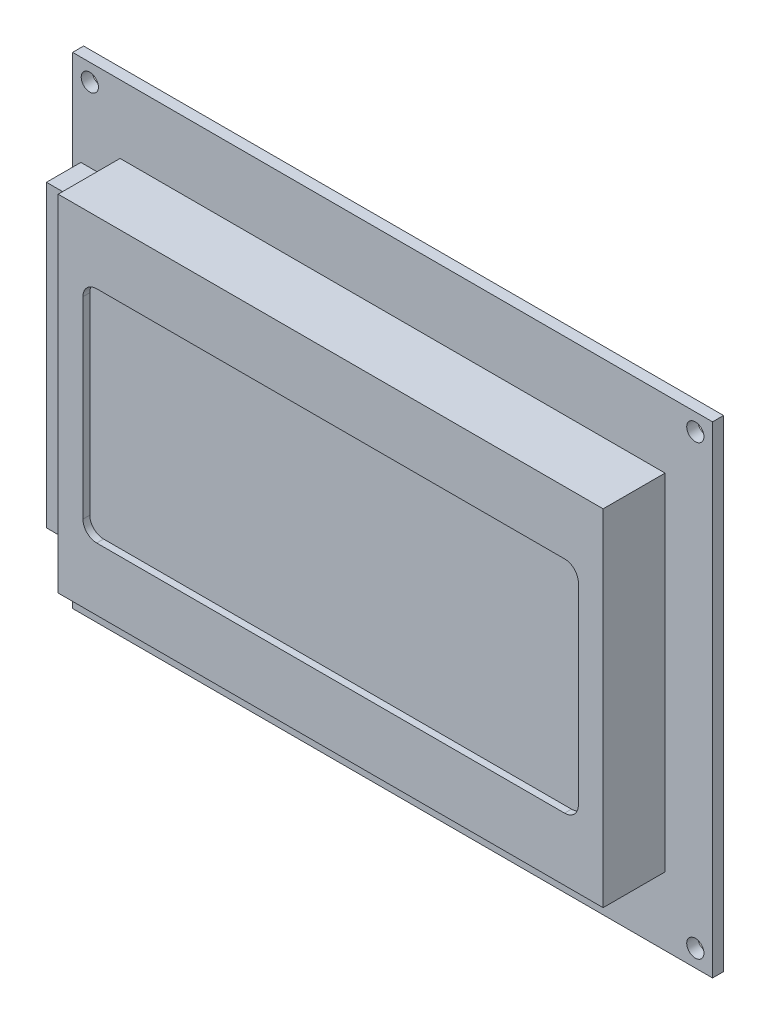
SolidWorks part; units mm, degrees
ref_plane "Plano frontal" through (0, 0, 0) normal (0, 0, 1) x (1, 0, 0)
ref_plane "Plano superior" through (0, 0, 0) normal (0, 1, 0) x (1, 0, 0)
ref_plane "Plano direito" through (0, 0, 0) normal (1, 0, 0) x (0, 0, -1)
sketch "Esboço1" plane through (0, 0, 0) normal (0, 0, 1) x (1, 0, 0)
  line L0 (-35, -33) -> (13.26, -33) construction
  line L1 (-46.5, -35) -> (46.5, -35)
  line L2 (-46.5, -35) -> (-46.5, 35)
  line L3 (-46.5, 35) -> (46.5, 35)
  line L4 (46.5, -35) -> (46.5, 35)
  line L5 (-46.5, -35) -> (46.5, 35) construction
  line L6 (-46.5, 35) -> (46.5, -35) construction
  line L7 (-44, -32.5) -> (44, -32.5) construction
  line L8 (-44, -32.5) -> (-44, 32.5) construction
  line L9 (-44, 32.5) -> (44, 32.5) construction
  line L10 (44, -32.5) -> (44, 32.5) construction
  line L11 (-44, -32.5) -> (44, 32.5) construction
  line L12 (-44, 32.5) -> (44, -32.5) construction
  line L13 (-39.6, -25.1) -> (39.6, -25.1)
  line L14 (-39.6, -25.1) -> (-39.6, 25.1)
  line L15 (-39.6, 25.1) -> (39.6, 25.1)
  line L16 (39.6, -25.1) -> (39.6, 25.1)
  line L17 (-39.6, -25.1) -> (39.6, 25.1) construction
  line L18 (-39.6, 25.1) -> (39.6, -25.1) construction
  line L19 (-34, -16) -> (34, -16)
  line L20 (-36, -14) -> (-36, 14)
  line L21 (-34, 16) -> (34, 16)
  line L22 (36, -14) -> (36, 14)
  line L23 (-36, -16) -> (36, 16) construction
  line L24 (-36, 16) -> (36, -16) construction
  line L26 (-45.3, -21.75) -> (-39.6, -21.75)
  line L27 (-45.3, -21.75) -> (-45.3, 21.75)
  line L28 (-45.3, 21.75) -> (-39.6, 21.75)
  line L29 (-39.6, -21.75) -> (-39.6, 21.75)
  line L30 (-45.3, -21.75) -> (-39.6, 21.75) construction
  line L31 (-45.3, 21.75) -> (-39.6, -21.75) construction
  circle A0 centre (-44, 32.5) radius 1.25
  circle A1 centre (44, 32.5) radius 1.25
  circle A2 centre (44, -32.5) radius 1.25
  circle A3 centre (-44, -32.5) radius 1.25
  arc A4 (-34, 16) -> (-36, 14) centre (-34, 14) ccw
  arc A5 (36, 14) -> (34, 16) centre (34, 14) ccw
  arc A6 (36, -14) -> (34, -16) centre (34, -14) cw
  arc A7 (-34, -16) -> (-36, -14) centre (-34, -14) cw
  circle A8 centre (-35, -33) radius 0.5
  circle A9 centre (13.26, -33) radius 0.5
  circle A10 centre (-32.46, -33) radius 0.5
  circle A11 centre (-29.92, -33) radius 0.5
  circle A12 centre (-27.38, -33) radius 0.5
  circle A13 centre (-24.84, -33) radius 0.5
  circle A14 centre (-22.3, -33) radius 0.5
  circle A15 centre (-19.76, -33) radius 0.5
  circle A16 centre (-17.22, -33) radius 0.5
  circle A17 centre (-14.68, -33) radius 0.5
  circle A18 centre (-12.14, -33) radius 0.5
  circle A19 centre (-9.6, -33) radius 0.5
  circle A20 centre (-7.06, -33) radius 0.5
  circle A21 centre (-4.52, -33) radius 0.5
  circle A22 centre (-1.98, -33) radius 0.5
  circle A23 centre (0.56, -33) radius 0.5
  circle A24 centre (3.1, -33) radius 0.5
  circle A25 centre (5.64, -33) radius 0.5
  circle A26 centre (8.18, -33) radius 0.5
  circle A27 centre (10.72, -33) radius 0.5
  point P0 (0, 0)
  point P7 (0, 0)
  point P8 (0, 0)
  point P16 (0, 0)
  point P21 (0, 0)
  point P78 (-42.45, 0)
  dimension "D5" = 2.5
  dimension "D6" = 2.5
  dimension "D7" = 2.5
  dimension "D8" = 2.5
  dimension "D13" = 2
  dimension "D14" = 2
  dimension "D15" = 2
  dimension "D16" = 2
  dimension "D17" = 11.5
  dimension "D18" = 2
  dimension "D19" = 1
  dimension "D21" = 1
  dimension "D22" = 2.54
  dimension "D23" = 2.54
  dimension "D24" = 2.54
  dimension "D25" = 2.54
  dimension "D26" = 2.54
  dimension "D27" = 1
  dimension "D28" = 1
  dimension "D29" = 1
  dimension "D30" = 1
  dimension "D31" = 1
  dimension "D32" = 2.54
  dimension "D33" = 2.54
  dimension "D34" = 2.54
  dimension "D45" = 1
  dimension "D46" = 1
  dimension "D47" = 1
  dimension "D48" = 1
  dimension "D49" = 1
  dimension "D50" = 1
  dimension "D51" = 1
  dimension "D52" = 1
  dimension "D53" = 1
  dimension "D54" = 1
  dimension "D55" = 1
  dimension "D56" = 1
  dimension "D57" = 1
  dimension "D1" = 70
  dimension "D2" = 93
  dimension "D3" = 88
  dimension "D4" = 65
  dimension "D9" = 79.2
  dimension "D10" = 50.2
  dimension "D11" = 72
  dimension "D12" = 32
  dimension "D20" = 48.26
  dimension "D35" = 2.54
  dimension "D36" = 2.54
  dimension "D37" = 2.54
  dimension "D38" = 2.54
  dimension "D39" = 2.54
  dimension "D40" = 2.54
  dimension "D41" = 2.54
  dimension "D42" = 2.54
  dimension "D43" = 2.54
  dimension "D44" = 2.54
  dimension "D58" = 5.7
  dimension "D59" = 43.5
extrude "Boss-Extrude1" add sketch "Esboço1" along normal blind 8 contours A7 L19 A6 L22 A5 L21 A4 L20
sketch "Sketch1" plane through (0, 0, 0) normal (0, 0, 1) x (1, 0, 0)
  line L0 (-35, -33) -> (13.26, -33) construction
  line L1 (-46.5, -35) -> (46.5, -35)
  line L2 (-46.5, -35) -> (-46.5, 35)
  line L3 (-46.5, 35) -> (46.5, 35)
  line L4 (46.5, -35) -> (46.5, 35)
  line L5 (-46.5, -35) -> (46.5, 35) construction
  line L6 (-46.5, 35) -> (46.5, -35) construction
  line L7 (-44, -32.5) -> (44, -32.5) construction
  line L8 (-44, -32.5) -> (-44, 32.5) construction
  line L9 (-44, 32.5) -> (44, 32.5) construction
  line L10 (44, -32.5) -> (44, 32.5) construction
  line L11 (-44, -32.5) -> (44, 32.5) construction
  line L12 (-44, 32.5) -> (44, -32.5) construction
  line L13 (-39.6, -25.1) -> (39.6, -25.1)
  line L14 (-39.6, -25.1) -> (-39.6, 25.1)
  line L15 (-39.6, 25.1) -> (39.6, 25.1)
  line L16 (39.6, -25.1) -> (39.6, 25.1)
  line L17 (-39.6, -25.1) -> (39.6, 25.1) construction
  line L18 (-39.6, 25.1) -> (39.6, -25.1) construction
  line L19 (-34, -16) -> (34, -16)
  line L20 (-36, -14) -> (-36, 14)
  line L21 (-34, 16) -> (34, 16)
  line L22 (36, -14) -> (36, 14)
  line L23 (-36, -16) -> (36, 16) construction
  line L24 (-36, 16) -> (36, -16) construction
  line L25 (-45.3, -21.75) -> (-39.6, -21.75)
  line L26 (-45.3, -21.75) -> (-45.3, 21.75)
  line L27 (-45.3, 21.75) -> (-39.6, 21.75)
  line L28 (-39.6, -21.75) -> (-39.6, 21.75)
  line L29 (-45.3, -21.75) -> (-39.6, 21.75) construction
  line L30 (-45.3, 21.75) -> (-39.6, -21.75) construction
  circle A0 centre (-44, 32.5) radius 1.25
  circle A1 centre (44, 32.5) radius 1.25
  circle A2 centre (44, -32.5) radius 1.25
  circle A3 centre (-44, -32.5) radius 1.25
  arc A4 (-34, 16) -> (-36, 14) centre (-34, 14) ccw
  arc A5 (36, 14) -> (34, 16) centre (34, 14) ccw
  arc A6 (36, -14) -> (34, -16) centre (34, -14) cw
  arc A7 (-34, -16) -> (-36, -14) centre (-34, -14) cw
  circle A8 centre (-35, -33) radius 0.5
  circle A9 centre (13.26, -33) radius 0.5
  circle A10 centre (-32.46, -33) radius 0.5
  circle A11 centre (-29.92, -33) radius 0.5
  circle A12 centre (-27.38, -33) radius 0.5
  circle A13 centre (-24.84, -33) radius 0.5
  circle A14 centre (-22.3, -33) radius 0.5
  circle A15 centre (-19.76, -33) radius 0.5
  circle A16 centre (-17.22, -33) radius 0.5
  circle A17 centre (-14.68, -33) radius 0.5
  circle A18 centre (-12.14, -33) radius 0.5
  circle A19 centre (-9.6, -33) radius 0.5
  circle A20 centre (-7.06, -33) radius 0.5
  circle A21 centre (-4.52, -33) radius 0.5
  circle A22 centre (-1.98, -33) radius 0.5
  circle A23 centre (0.56, -33) radius 0.5
  circle A24 centre (3.1, -33) radius 0.5
  circle A25 centre (5.64, -33) radius 0.5
  circle A26 centre (8.18, -33) radius 0.5
  circle A27 centre (10.72, -33) radius 0.5
  point P0 (0, 0)
  point P6 (0, 0)
  point P7 (0, 0)
  point P15 (0, 0)
  point P20 (0, 0)
  point P77 (-42.45, 0)
  dimension "D5" = 2.5
  dimension "D6" = 2.5
  dimension "D7" = 2.5
  dimension "D8" = 2.5
  dimension "D13" = 2
  dimension "D14" = 2
  dimension "D15" = 2
  dimension "D16" = 2
  dimension "D19" = 1
  dimension "D21" = 1
  dimension "D27" = 1
  dimension "D28" = 1
  dimension "D29" = 1
  dimension "D30" = 1
  dimension "D31" = 1
  dimension "D45" = 1
  dimension "D46" = 1
  dimension "D47" = 1
  dimension "D48" = 1
  dimension "D49" = 1
  dimension "D50" = 1
  dimension "D51" = 1
  dimension "D52" = 1
  dimension "D53" = 1
  dimension "D54" = 1
  dimension "D55" = 1
  dimension "D56" = 1
  dimension "D57" = 1
  dimension "D1" = 70
  dimension "D2" = 93
  dimension "D3" = 88
  dimension "D4" = 65
  dimension "D9" = 79.2
  dimension "D10" = 50.2
  dimension "D11" = 72
  dimension "D12" = 32
  dimension "D17" = 11.5
  dimension "D18" = 2
  dimension "D20" = 48.26
  dimension "D22" = 2.54
  dimension "D23" = 2.54
  dimension "D24" = 2.54
  dimension "D25" = 2.54
  dimension "D26" = 2.54
  dimension "D32" = 2.54
  dimension "D33" = 2.54
  dimension "D34" = 2.54
  dimension "D35" = 2.54
  dimension "D36" = 2.54
  dimension "D37" = 2.54
  dimension "D38" = 2.54
  dimension "D39" = 2.54
  dimension "D40" = 2.54
  dimension "D41" = 2.54
  dimension "D42" = 2.54
  dimension "D43" = 2.54
  dimension "D44" = 2.54
  dimension "D58" = 5.7
  dimension "D59" = 43.5
extrude "Boss-Extrude2" add sketch "Sketch1" along normal blind 9 contours L13 L16 L15 L14 L19 A7 L20 A4 L21 A5 L22 A6
sketch "Sketch2" plane through (0, 0, 0) normal (0, 0, 1) x (1, 0, 0)
  line L0 (-35, -33) -> (13.26, -33) construction
  line L1 (-46.5, -35) -> (46.5, -35)
  line L2 (-46.5, -35) -> (-46.5, 35)
  line L3 (-46.5, 35) -> (46.5, 35)
  line L4 (46.5, -35) -> (46.5, 35)
  line L7 (-44, -32.5) -> (44, -32.5) construction
  line L8 (-44, -32.5) -> (-44, 32.5) construction
  line L9 (-44, 32.5) -> (44, 32.5) construction
  line L10 (44, -32.5) -> (44, 32.5) construction
  circle A0 centre (-44, 32.5) radius 1.25
  circle A1 centre (44, 32.5) radius 1.25
  circle A2 centre (44, -32.5) radius 1.25
  circle A3 centre (-44, -32.5) radius 1.25
  circle A8 centre (-35, -33) radius 0.5
  circle A9 centre (13.26, -33) radius 0.5
  circle A10 centre (-32.46, -33) radius 0.5
  circle A11 centre (-29.92, -33) radius 0.5
  circle A12 centre (-27.38, -33) radius 0.5
  circle A13 centre (-24.84, -33) radius 0.5
  circle A14 centre (-22.3, -33) radius 0.5
  circle A15 centre (-19.76, -33) radius 0.5
  circle A16 centre (-17.22, -33) radius 0.5
  circle A17 centre (-14.68, -33) radius 0.5
  circle A18 centre (-12.14, -33) radius 0.5
  circle A19 centre (-9.6, -33) radius 0.5
  circle A20 centre (-7.06, -33) radius 0.5
  circle A21 centre (-4.52, -33) radius 0.5
  circle A22 centre (-1.98, -33) radius 0.5
  circle A23 centre (0.56, -33) radius 0.5
  circle A24 centre (3.1, -33) radius 0.5
  circle A25 centre (5.64, -33) radius 0.5
  circle A26 centre (8.18, -33) radius 0.5
  circle A27 centre (10.72, -33) radius 0.5
  point P77 (-42.45, 0)
  dimension "D5" = 2.5
  dimension "D6" = 2.5
  dimension "D7" = 2.5
  dimension "D8" = 2.5
  dimension "D19" = 1
  dimension "D21" = 1
  dimension "D27" = 1
  dimension "D28" = 1
  dimension "D29" = 1
  dimension "D30" = 1
  dimension "D31" = 1
  dimension "D45" = 1
  dimension "D46" = 1
  dimension "D47" = 1
  dimension "D48" = 1
  dimension "D49" = 1
  dimension "D50" = 1
  dimension "D51" = 1
  dimension "D52" = 1
  dimension "D53" = 1
  dimension "D54" = 1
  dimension "D55" = 1
  dimension "D56" = 1
  dimension "D57" = 1
  dimension "D1" = 70
  dimension "D2" = 93
  dimension "D3" = 88
  dimension "D4" = 65
  dimension "D17" = 11.5
  dimension "D18" = 2
  dimension "D20" = 48.26
  dimension "D22" = 2.54
  dimension "D23" = 2.54
  dimension "D24" = 2.54
  dimension "D25" = 2.54
  dimension "D26" = 2.54
  dimension "D32" = 2.54
  dimension "D33" = 2.54
  dimension "D34" = 2.54
  dimension "D35" = 2.54
  dimension "D36" = 2.54
  dimension "D37" = 2.54
  dimension "D38" = 2.54
  dimension "D39" = 2.54
  dimension "D40" = 2.54
  dimension "D41" = 2.54
  dimension "D42" = 2.54
  dimension "D43" = 2.54
  dimension "D44" = 2.54
extrude "Boss-Extrude3" add sketch "Sketch2" against normal blind 1.6 separate body contours L1 L4 L3 L2 A27 A26 A25 A24 A23 A22 A21 A20 A19 A18 A17 A16 A15 A14 A13 A12 A11 A10 A9 A8 A3 A2 A1
sketch "Sketch3" plane through (0, 0, 0) normal (0, 0, 1) x (1, 0, 0)
  line L0 (-35, -33) -> (13.26, -33) construction
  line L1 (-46.5, -35) -> (46.5, -35)
  line L2 (-46.5, -35) -> (-46.5, 35)
  line L3 (-46.5, 35) -> (46.5, 35)
  line L4 (46.5, -35) -> (46.5, 35)
  line L5 (-46.5, -35) -> (46.5, 35) construction
  line L6 (-46.5, 35) -> (46.5, -35) construction
  line L7 (-44, -32.5) -> (44, -32.5) construction
  line L8 (-44, -32.5) -> (-44, 32.5) construction
  line L9 (-44, 32.5) -> (44, 32.5) construction
  line L10 (44, -32.5) -> (44, 32.5) construction
  line L11 (-44, -32.5) -> (44, 32.5) construction
  line L12 (-44, 32.5) -> (44, -32.5) construction
  line L13 (-39.6, -25.1) -> (39.6, -25.1)
  line L14 (-39.6, -25.1) -> (-39.6, 25.1)
  line L15 (-39.6, 25.1) -> (39.6, 25.1)
  line L16 (39.6, -25.1) -> (39.6, 25.1)
  line L17 (-39.6, -25.1) -> (39.6, 25.1) construction
  line L18 (-39.6, 25.1) -> (39.6, -25.1) construction
  line L19 (-34, -16) -> (34, -16)
  line L20 (-36, -14) -> (-36, 14)
  line L21 (-34, 16) -> (34, 16)
  line L22 (36, -14) -> (36, 14)
  line L23 (-36, -16) -> (36, 16) construction
  line L24 (-36, 16) -> (36, -16) construction
  line L25 (-45.3, -21.75) -> (-39.6, -21.75)
  line L26 (-45.3, -21.75) -> (-45.3, 21.75)
  line L27 (-45.3, 21.75) -> (-39.6, 21.75)
  line L28 (-39.6, -21.75) -> (-39.6, 21.75)
  line L29 (-45.3, -21.75) -> (-39.6, 21.75) construction
  line L30 (-45.3, 21.75) -> (-39.6, -21.75) construction
  circle A0 centre (-44, 32.5) radius 1.25
  circle A1 centre (44, 32.5) radius 1.25
  circle A2 centre (44, -32.5) radius 1.25
  circle A3 centre (-44, -32.5) radius 1.25
  arc A4 (-34, 16) -> (-36, 14) centre (-34, 14) ccw
  arc A5 (36, 14) -> (34, 16) centre (34, 14) ccw
  arc A6 (36, -14) -> (34, -16) centre (34, -14) cw
  arc A7 (-34, -16) -> (-36, -14) centre (-34, -14) cw
  circle A8 centre (-35, -33) radius 0.5
  circle A9 centre (13.26, -33) radius 0.5
  circle A10 centre (-32.46, -33) radius 0.5
  circle A11 centre (-29.92, -33) radius 0.5
  circle A12 centre (-27.38, -33) radius 0.5
  circle A13 centre (-24.84, -33) radius 0.5
  circle A14 centre (-22.3, -33) radius 0.5
  circle A15 centre (-19.76, -33) radius 0.5
  circle A16 centre (-17.22, -33) radius 0.5
  circle A17 centre (-14.68, -33) radius 0.5
  circle A18 centre (-12.14, -33) radius 0.5
  circle A19 centre (-9.6, -33) radius 0.5
  circle A20 centre (-7.06, -33) radius 0.5
  circle A21 centre (-4.52, -33) radius 0.5
  circle A22 centre (-1.98, -33) radius 0.5
  circle A23 centre (0.56, -33) radius 0.5
  circle A24 centre (3.1, -33) radius 0.5
  circle A25 centre (5.64, -33) radius 0.5
  circle A26 centre (8.18, -33) radius 0.5
  circle A27 centre (10.72, -33) radius 0.5
  point P0 (0, 0)
  point P6 (0, 0)
  point P7 (0, 0)
  point P15 (0, 0)
  point P20 (0, 0)
  point P77 (-42.45, 0)
  dimension "D5" = 2.5
  dimension "D6" = 2.5
  dimension "D7" = 2.5
  dimension "D8" = 2.5
  dimension "D13" = 2
  dimension "D14" = 2
  dimension "D15" = 2
  dimension "D16" = 2
  dimension "D19" = 1
  dimension "D21" = 1
  dimension "D27" = 1
  dimension "D28" = 1
  dimension "D29" = 1
  dimension "D30" = 1
  dimension "D31" = 1
  dimension "D45" = 1
  dimension "D46" = 1
  dimension "D47" = 1
  dimension "D48" = 1
  dimension "D49" = 1
  dimension "D50" = 1
  dimension "D51" = 1
  dimension "D52" = 1
  dimension "D53" = 1
  dimension "D54" = 1
  dimension "D55" = 1
  dimension "D56" = 1
  dimension "D57" = 1
  dimension "D1" = 70
  dimension "D2" = 93
  dimension "D3" = 88
  dimension "D4" = 65
  dimension "D9" = 79.2
  dimension "D10" = 50.2
  dimension "D11" = 72
  dimension "D12" = 32
  dimension "D17" = 11.5
  dimension "D18" = 2
  dimension "D20" = 48.26
  dimension "D22" = 2.54
  dimension "D23" = 2.54
  dimension "D24" = 2.54
  dimension "D25" = 2.54
  dimension "D26" = 2.54
  dimension "D32" = 2.54
  dimension "D33" = 2.54
  dimension "D34" = 2.54
  dimension "D35" = 2.54
  dimension "D36" = 2.54
  dimension "D37" = 2.54
  dimension "D38" = 2.54
  dimension "D39" = 2.54
  dimension "D40" = 2.54
  dimension "D41" = 2.54
  dimension "D42" = 2.54
  dimension "D43" = 2.54
  dimension "D44" = 2.54
  dimension "D58" = 5.7
  dimension "D59" = 43.5
extrude "Boss-Extrude4" add sketch "Sketch3" along normal blind 5 contours L27 L26 L25 L14
